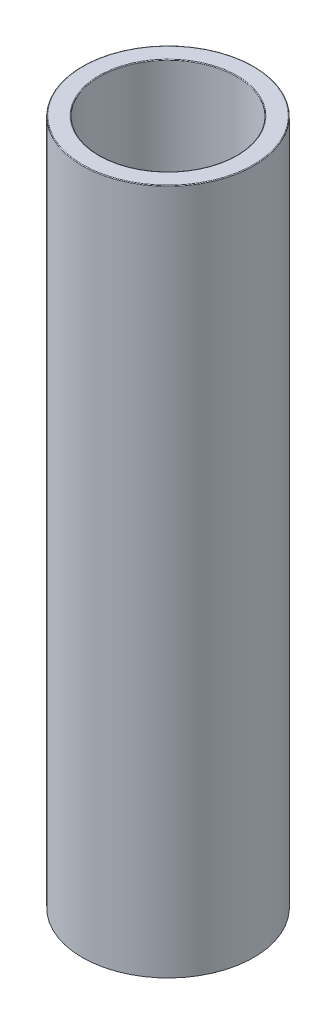
SolidWorks part; units mm, degrees
ref_plane "Front Plane" through (0, 0, 0) normal (0, 0, 1) x (1, 0, 0)
ref_plane "Top Plane" through (0, 0, 0) normal (0, 1, 0) x (1, 0, 0)
ref_plane "Right Plane" through (0, 0, 0) normal (1, 0, 0) x (0, 0, -1)
sketch "Sketch1" plane through (0, 0, 0) normal (0, 1, 0) x (1, 0, 0)
  circle A0 centre (0, 0) radius 1
  circle A1 centre (0, 0) radius 1.25
  dimension "D1" = 2.5
  dimension "D2" = 2
extrude "Boss-Extrude1" add sketch "Sketch1" along normal blind 10
fillet "Fillet1" radius 0.01 3 edges at (0, 10, 1.25) (0, 0, 1) (0, 10, 1)
